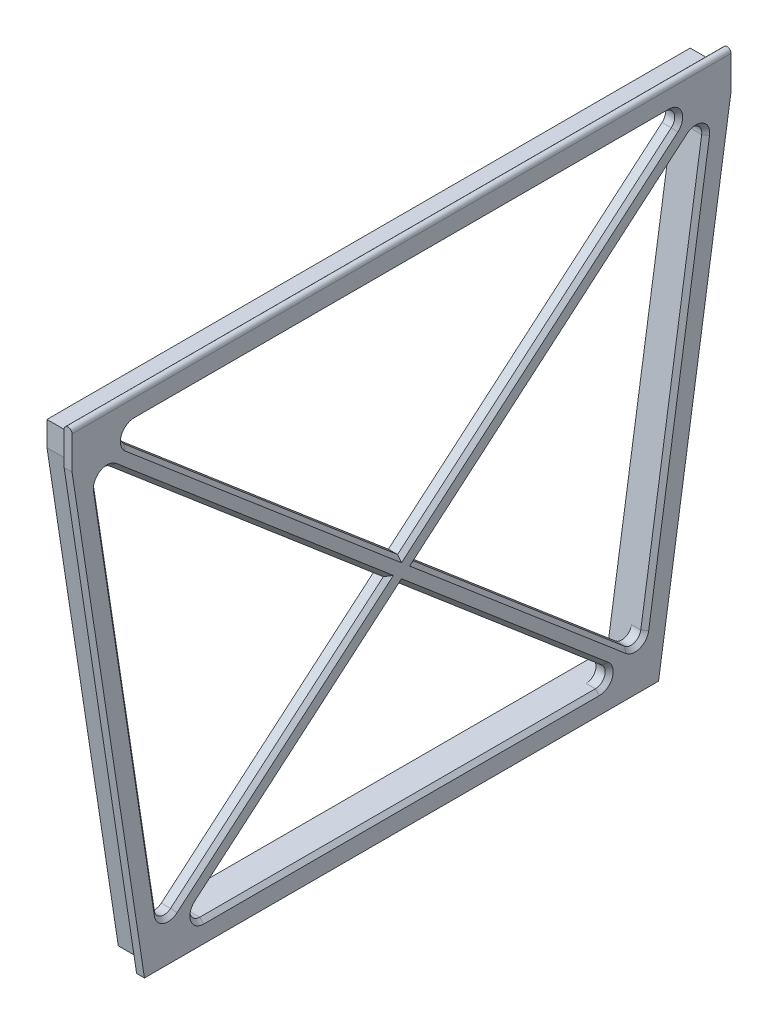
SolidWorks part; units mm, degrees
ref_plane "Front Plane" through (0, 0, 0) normal (0, 0, 1) x (1, 0, 0)
ref_plane "Top Plane" through (0, 0, 0) normal (0, 1, 0) x (1, 0, 0)
ref_plane "Right Plane" through (0, 0, 0) normal (1, 0, 0) x (0, 0, -1)
sketch "Sketch1" plane through (0, 0, 0) normal (1, 0, 0) x (0, 0, -1)
  line L0 (-39, 0) -> (39, 0)
  line L1 (39, 0) -> (50, 72)
  line L2 (50, 72) -> (-50, 72) construction
  line L3 (-50, 72) -> (-39, 0)
  line L4 (0, 72) -> (0, 0) construction
  line L5 (-50, 72) -> (-50, 77)
  line L6 (-50, 77) -> (50, 77)
  line L7 (50, 77) -> (50, 72)
  point P7 (0, 0)
  dimension "D1" = 5
  dimension "D2" = 100
  dimension "D3" = 78
  dimension "D4" = 72
extrude "Extrude-Thin1" add sketch "Sketch1" along normal blind 5 thin thin type one direction reverse wall 3.2
sketch "Sketch3" plane through (5, 0, 0) normal (1, 0, 0) x (0, 0, -1)
  line L0 (-46.8, 73.8) -> (36.2518, 3.2)
  line L1 (46.8, 73.8) -> (-36.2518, 3.2)
  point P2 (-47.0481, 73.2206)
  point P6 (46.8824, 73.9126)
extrude "Extrude-Thin2" add sketch "Sketch3" against normal blind 2 thin thin type mid plane wall 2.8
sketch "Sketch4" plane through (0, 0, 0) normal (-1, 0, 0) x (0, 0, 1)
  line L0 (50, 72) -> (39, 0) construction
  line L1 (39, 0) -> (-39, 0) construction
  line L2 (-39, 0) -> (-50, 72) construction
  line L3 (50, 72) -> (39, 0)
  line L4 (39, 0) -> (-39, 0)
  line L5 (-39, 0) -> (-50, 72)
  line L6 (50, 77) -> (50, 72) construction
  line L7 (-50, 72) -> (-50, 77) construction
  line L8 (50, 77) -> (50, 72)
  line L9 (-50, 72) -> (-50, 77)
  line L10 (-50, 77) -> (50, 77) construction
  line L11 (-50, 77) -> (50, 77)
extrude "Cut-Extrude-Thin1" cut sketch "Sketch4" against normal offset from surface 1.2 and the other way through all thin
sketch "Sketch5" plane through (0, 0, -50) normal (0, 0, -1) x (-1, 0, 0)
  line L0 (-5, 77) -> (-3.8, 77) construction
  line L1 (-5, 77) -> (-3.8, 77)
  arc A0 (-5, 77) -> (-3.8, 77) centre (-4.4, 77) cw
extrude "Boss-Extrude1" add sketch "Sketch5" against normal up to surface (100 mm away) up to face at (4.4, 74.5, 50)
fillet "Fillet1" radius 1.5 8 edges at (4, 3.2, -34.0902) (4, 4.8263, -36.5002) (4, 4.8263, 36.5002) (4, 3.2, 34.0902) (4, 71.9206, 46.7507) (4, 73.8, 44.6384) (4, 71.9206, -46.7507) (4, 73.8, -44.6384)
chamfer "Chamfer1" distance 0.6 angle 45 20 edges at (5, 37.7165, -41.5251) (5, 3.2, 0) (5, 37.7165, 41.5251) (5, 73.8, 0) (5, 20.292, -18.3067) (5, 51.6676, -22.9256) (5, 6.3051, -35.9481) (5, 69.4855, -45.3921) (5, 19.011, 15.4906) (5, 19.011, -15.4906) (5, 4.1825, 31.4176) (5, 4.1825, -31.4176) (5, 51.6676, 22.9256) (5, 20.292, 18.3067) (5, 69.4855, 45.3921) (5, 6.3051, 35.9481) (5, 53.5056, -20.7647) (5, 53.5056, 20.7647) (5, 72.8175, -41.9658) (5, 72.8175, 41.9658)
